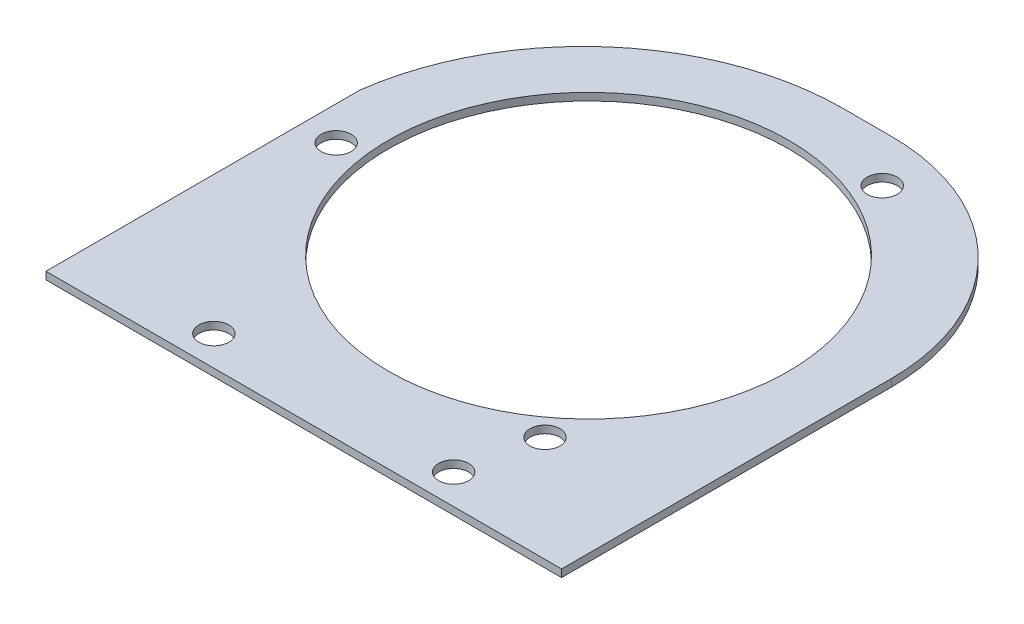
SolidWorks part; units mm, degrees
ref_plane "Front Plane" through (0, 0, 0) normal (0, 0, 1) x (1, 0, 0)
ref_plane "Top Plane" through (0, 0, 0) normal (0, 1, 0) x (1, 0, 0)
ref_plane "Right Plane" through (0, 0, 0) normal (1, 0, 0) x (0, 0, -1)
sketch "Sketch1" plane through (0, 0, 0) normal (0, 1, 0) x (1, 0, 0)
  line L0 (-3.5683, 110.5657) -> (-3.5683, -118.0343) construction
  line L1 (16.7517, 110.5657) -> (-3.5683, 110.5657)
  line L2 (105.6517, 21.6657) -> (105.6517, -118.0343)
  line L3 (105.6517, -118.0343) -> (-112.7883, -118.0343)
  line L4 (-112.7883, 14.9422) -> (-112.7883, -118.0343)
  line L5 (105.6517, 110.5657) -> (-112.7883, -118.0343) construction
  line L6 (105.6517, -118.0343) -> (-97.5421, 108.9743) construction
  line L7 (-112.7883, 2.6157) -> (105.6517, 2.6157) construction
  line L8 (-3.5683, 2.6157) -> (-112.7883, -34.9918) construction
  line L9 (-112.7883, -105.3343) -> (105.6517, -105.3343) construction
  circle A0 centre (-3.5683, 2.6157) radius 84.7725
  circle A1 centre (-3.5683, 2.6157) radius 95.25 construction
  circle A2 centre (-98.4365, -9.4505) radius 6.35
  circle A3 centre (-54.3683, -105.3343) radius 6.35
  circle A4 centre (47.2317, -105.3343) radius 6.35
  circle A5 centre (32.9548, 90.5211) radius 6.35
  circle A6 centre (53.8372, -73.2529) radius 6.35
  arc A7 (-3.5683, 110.5657) -> (-112.7883, 14.9422) centre (-3.5683, 0.3791) ccw
  arc A8 (16.7517, 110.5657) -> (105.6517, 21.6657) centre (16.7517, 21.6657) cw
  circle A9 centre (-98.4365, -9.4505) radius 6.35 construction
  circle A10 centre (32.9548, 90.5211) radius 6.35 construction
  circle A12 centre (-3.5683, 2.6157) radius 84.7725 construction
  point P0 (0, 0)
  point P11 (-3.5683, 2.6157)
  point P30 (-3.8815, 2.6059)
  point P32 (0, 6.35)
  dimension "D3" = 109.22
  dimension "D5" = 190.5
  dimension "D6" = 12.7
  dimension "D7" = 12.7
  dimension "D8" = 12.7
  dimension "D11" = 3
  dimension "D1" = 228.6
  dimension "D2" = 120.65
  dimension "D4" = 19
  dimension "D9" = 50.8
  dimension "D10" = 203.2
extrude "Boss-Extrude1" add sketch "Sketch1" along normal blind 3.175
sketch "Sketch2" plane through (0, 3.175, 0) normal (0, 1, 0) x (1, 0, 0)
  line L0 (-112.7883, 14.9422) -> (-112.7883, -118.0343) construction
  line L2 (105.6517, -171.3743) -> (-112.7883, -171.3743)
  line L5 (105.6517, -171.3743) -> (105.6517, 110.5657)
  line L6 (105.6517, 110.5657) -> (-112.7883, 110.5657)
  line L7 (-112.7883, -118.0343) -> (105.6517, -118.0343) construction
  line L8 (105.6517, -118.0343) -> (105.6517, 21.6657) construction
  line L9 (16.7517, 110.5657) -> (-3.5683, 110.5657) construction
  line L10 (-112.7883, 14.9422) -> (-112.7883, -118.0343)
  line L11 (-112.7883, -118.0343) -> (105.6517, -118.0343)
  line L12 (105.6517, -118.0343) -> (105.6517, 21.6657)
  line L13 (16.7517, 110.5657) -> (-3.5683, 110.5657)
  line L14 (-112.7883, -171.3743) -> (-112.7883, 110.5657)
  line L15 (105.6517, -171.3743) -> (-135.6483, -171.3743)
  line L16 (105.6517, -171.3743) -> (105.6517, 111.6071)
  line L17 (105.6517, 111.6071) -> (-135.6483, 111.6071)
  line L18 (-135.6483, -171.3743) -> (-135.6483, 111.6071)
  point P0 (0, 0)
  dimension "D1" = 1.0414
  dimension "D2" = 53.34
  dimension "D3" = 228.6
  dimension "D4" = 218.44
  dimension "D5" = 241.3
  dimension "D6" = 282.9814
